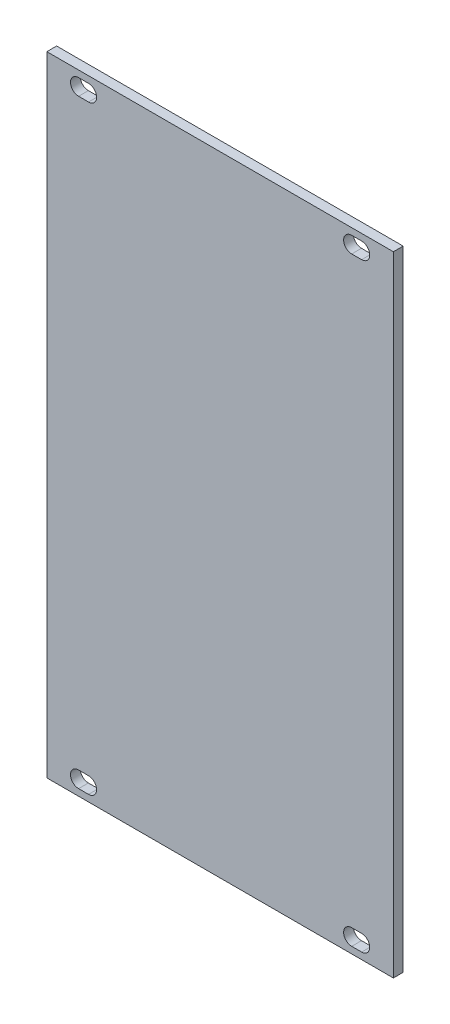
SolidWorks part; units mm, degrees
ref_plane "Front Plane" through (0, 0, 0) normal (0, 0, 1) x (1, 0, 0)
ref_plane "Top Plane" through (0, 0, 0) normal (0, 1, 0) x (1, 0, 0)
ref_plane "Right Plane" through (0, 0, 0) normal (1, 0, 0) x (0, 0, -1)
sketch "Sketch1" plane through (0, 0, 0) normal (0, 0, 1) x (1, 0, 0)
  line L0 (-27.9, 64.25) -> (-27.9, -64.25) construction
  line L1 (-35.4, 64.25) -> (35.4, 64.25)
  line L2 (-35.4, 64.25) -> (-35.4, -64.25)
  line L3 (-35.4, -64.25) -> (35.4, -64.25)
  line L4 (35.4, 64.25) -> (35.4, -64.25)
  line L5 (-35.4, 64.25) -> (35.4, -64.25) construction
  line L6 (-35.4, -64.25) -> (35.4, 64.25) construction
  line L7 (-35.4, 61.25) -> (35.4, 61.25) construction
  line L8 (-35.4, -61.25) -> (35.4, -61.25) construction
  line L9 (-28.916, -61.25) -> (-26.884, -61.25) construction
  line L10 (26.884, 61.25) -> (28.916, 61.25) construction
  line L11 (-28.916, -59.6) -> (-26.884, -59.6)
  line L12 (-28.916, -62.9) -> (-26.884, -62.9)
  line L13 (-28.916, 61.25) -> (-26.884, 61.25) construction
  line L14 (-28.916, 62.9) -> (-26.884, 62.9)
  line L15 (-28.916, 59.6) -> (-26.884, 59.6)
  line L16 (26.884, 62.9) -> (28.916, 62.9)
  line L17 (26.884, 59.6) -> (28.916, 59.6)
  line L18 (26.884, -61.25) -> (28.916, -61.25) construction
  line L19 (26.884, -59.6) -> (28.916, -59.6)
  line L20 (26.884, -62.9) -> (28.916, -62.9)
  line L21 (27.9, 64.25) -> (27.9, -64.25) construction
  arc A0 (-28.916, -59.6) -> (-28.916, -62.9) centre (-28.916, -61.25) ccw
  arc A1 (-26.884, -62.9) -> (-26.884, -59.6) centre (-26.884, -61.25) ccw
  arc A2 (-28.916, 62.9) -> (-28.916, 59.6) centre (-28.916, 61.25) ccw
  arc A3 (-26.884, 59.6) -> (-26.884, 62.9) centre (-26.884, 61.25) ccw
  arc A4 (26.884, 62.9) -> (26.884, 59.6) centre (26.884, 61.25) ccw
  arc A5 (28.916, 59.6) -> (28.916, 62.9) centre (28.916, 61.25) ccw
  arc A6 (26.884, -59.6) -> (26.884, -62.9) centre (26.884, -61.25) ccw
  arc A7 (28.916, -62.9) -> (28.916, -59.6) centre (28.916, -61.25) ccw
  point P0 (0, 0)
  point P8 (27.9, 61.25)
  point P18 (-27.9, -61.25)
  point P24 (-27.9, 61.25)
  point P34 (27.9, -61.25)
  point P42 (0, 0)
  point P43 (0, 0)
  dimension "D6" = 1.65
  dimension "D7" = 1.65
  dimension "D11" = 1.65
  dimension "D13" = 1.65
  dimension "D1" = 128.5
  dimension "D2" = 70.8
  dimension "D3" = 7.5
  dimension "D4" = 3
  dimension "D8" = 2.032
  dimension "D9" = 2.032
  dimension "D10" = 7.5
  dimension "D12" = 2.032
  dimension "D14" = 2.032
  dimension "D5" = 3
extrude "Boss-Extrude1" add sketch "Sketch1" along normal blind 2
